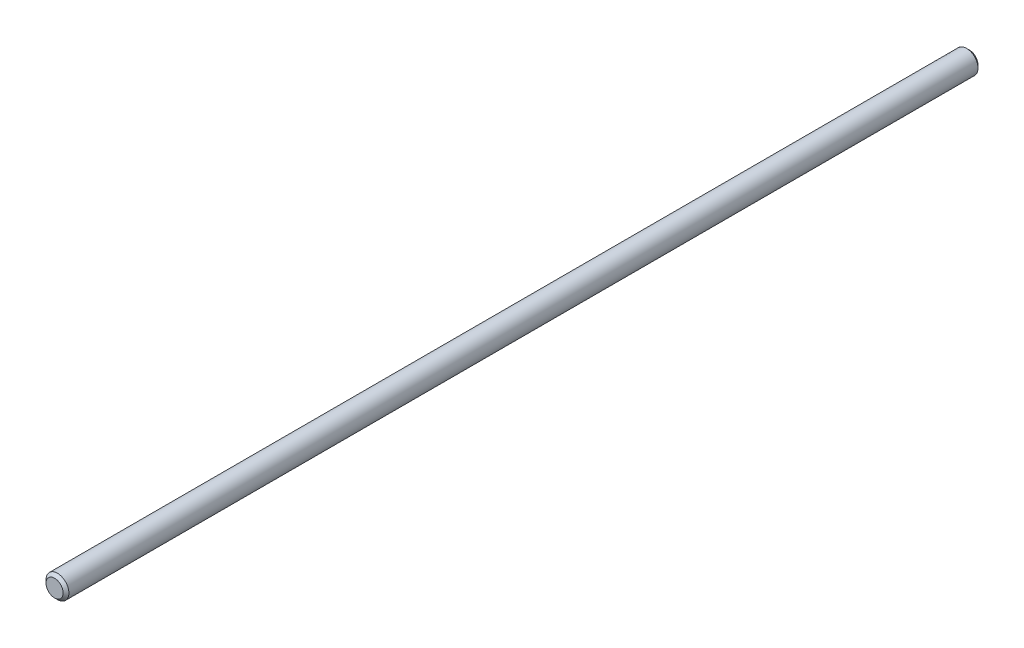
SolidWorks part; units mm, degrees
ref_plane "Front Plane" through (0, 0, 0) normal (0, 0, 1) x (1, 0, 0)
ref_plane "Top Plane" through (0, 0, 0) normal (0, 1, 0) x (1, 0, 0)
ref_plane "Right Plane" through (0, 0, 0) normal (1, 0, 0) x (0, 0, -1)
sketch "Sketch1" plane through (0, 0, 0) normal (0, 0, 1) x (1, 0, 0)
  circle A0 centre (0, 0) radius 2
  dimension "D1" = 4
extrude "Boss-Extrude1" add sketch "Sketch1" along normal mid plane 160
cosmetic thread "Cosmetic Thread5" parameters "D1"=10, "D2"=3.22
cosmetic thread "Cosmetic Thread6" parameters "D1"=8, "D2"=3.22
chamfer "Chamfer1" distance 0.5 angle 45 2 edges at (2, 0, 80) (2, 0, -80)
